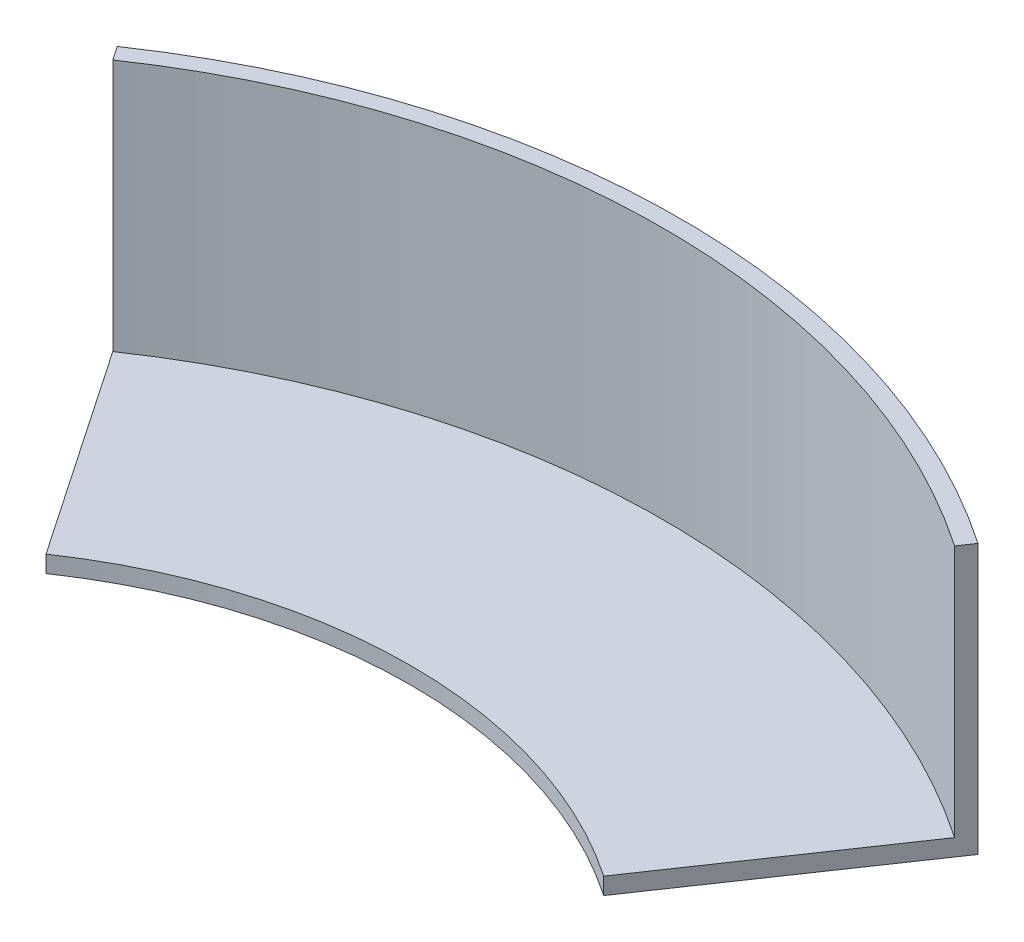
SolidWorks part; units mm, degrees
ref_plane "Front Plane" through (0, 0, 0) normal (0, 0, 1) x (1, 0, 0)
ref_plane "Top Plane" through (0, 0, 0) normal (0, 1, 0) x (1, 0, 0)
ref_plane "Right Plane" through (0, 0, 0) normal (1, 0, 0) x (0, 0, -1)
sketch "Sketch1" plane through (0, 0, 0) normal (0, 1, 0) x (1, 0, 0)
  line L0 (-36.7533, 25) -> (-50, 25)
  line L1 (-25, -50) -> (25, -50)
  line L2 (-25, -50) -> (-25, -36.7533)
  line L3 (-25, 50) -> (25, 50)
  line L4 (25, -50) -> (25, -36.7533)
  line L5 (-25, -50) -> (25, 50) construction
  line L6 (-25, 50) -> (25, -50) construction
  line L7 (50, -25) -> (36.7533, -25)
  line L8 (50, -25) -> (50, 25)
  line L9 (50, 25) -> (36.7533, 25)
  line L10 (-50, -25) -> (-50, 25)
  line L11 (50, -25) -> (-50, 25) construction
  line L12 (50, 25) -> (-50, -25) construction
  line L13 (-25, 36.7533) -> (-25, 50)
  line L14 (-36.7533, -25) -> (-50, -25)
  line L15 (8.0039, -25) -> (-8.0039, -25)
  line L16 (25, 36.7533) -> (25, 50)
  line L17 (8.0039, 25) -> (-8.0039, 25)
  line L18 (-25, 36.7533) -> (0, 0)
  line L19 (0, 0) -> (25, 36.7533)
  line L20 (25, 36.7533) -> (24.461, 36.4625)
  line L21 (36.7533, -25) -> (0, 0)
  line L22 (0, 0) -> (25, -36.7533)
  line L23 (25, -36.7533) -> (24.9892, -36.4366)
  line L24 (-25, -36.7533) -> (0, 0)
  line L25 (0, 0) -> (-36.7533, -25)
  line L27 (-36.7533, 25) -> (-37.6089, 25.105)
  line L28 (36.7533, 25) -> (0, 0)
  line L29 (-36.7533, 25) -> (0, 0)
  line L30 (-36.7533, -25) -> (0, 0)
  line L31 (-25, -36.7533) -> (0, 0)
  line L32 (24.9892, -36.4366) -> (0, 0)
  line L33 (0, 0) -> (0.1659, -0.3344)
  line L34 (36.7533, -25) -> (0.1659, -0.3344)
  circle A0 centre (0, 0) radius 26.25
  circle A1 centre (0, 0) radius 44.45
  circle A2 centre (0, 0) radius 29.45
  dimension "D1" = 52.5
  dimension "D2" = 88.9
  dimension "D7" = 15
  dimension "D3" = 50
  dimension "D4" = 50
  dimension "D5" = 100
  dimension "D6" = 100
extrude "Boss-Extrude1" add sketch "Sketch1" along normal blind 15
shell "Shell1" thickness 1
